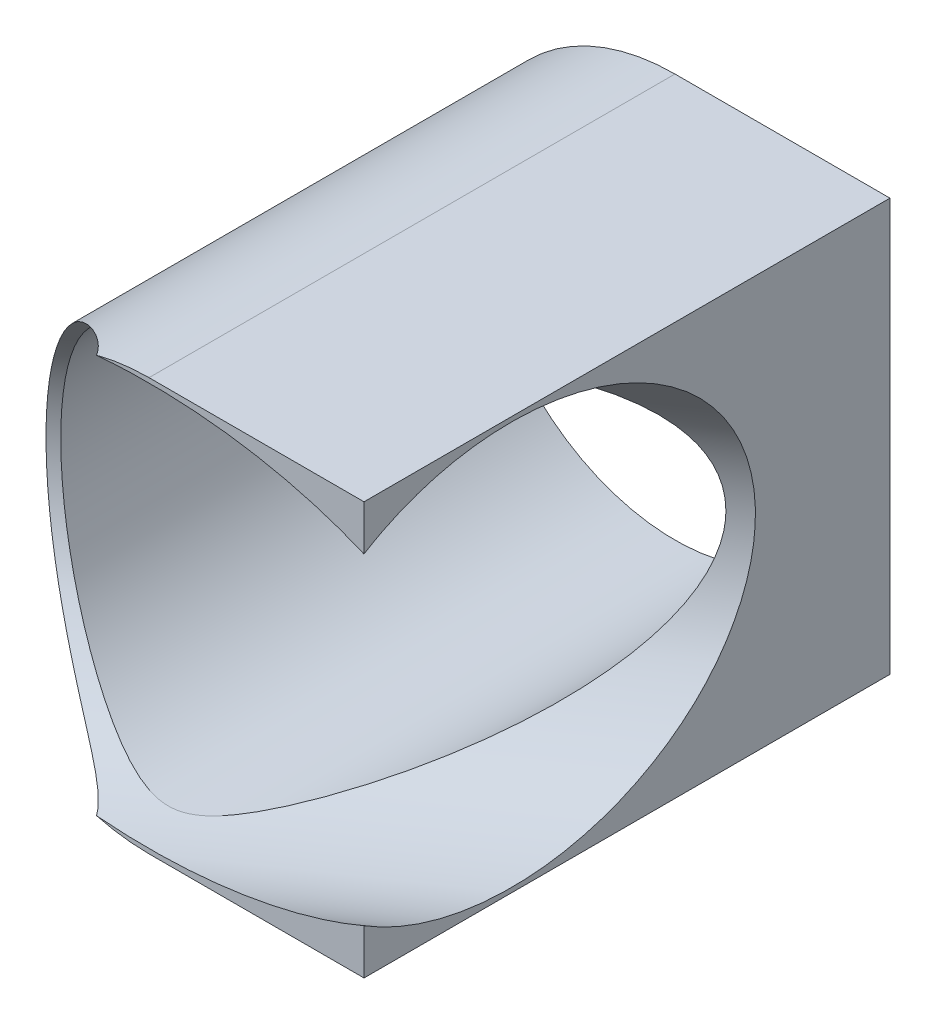
SolidWorks part; units mm, degrees
ref_plane "Front Plane" through (0, 0, 0) normal (0, 0, 1) x (1, 0, 0)
ref_plane "Top Plane" through (0, 0, 0) normal (0, 1, 0) x (1, 0, 0)
ref_plane "Right Plane" through (0, 0, 0) normal (1, 0, 0) x (0, 0, -1)
sketch "Sketch1" plane through (0, 0, 0) normal (0, 0, 1) x (1, 0, 0)
  circle A0 centre (443.1275, 0) radius 22.225 construction
  circle A1 centre (443.1275, 0) radius 22.225 construction
  circle A2 centre (443.1275, 0) radius 23.525
  circle A3 centre (443.1275, 0) radius 22.525
  dimension "D1" = 1.3
  dimension "D2" = 0.3
extrude "Boss-Extrude1" add sketch "Sketch1" against normal blind 60
sketch "Sketch3" plane through (0, 0, -60) normal (0, 0, -1) x (-1, 0, 0)
  line L0 (-443.1275, -23.525) -> (-466.6525, -23.525)
  line L1 (-466.6525, -23.525) -> (-466.6525, 0)
  line L2 (-466.6525, 0) -> (-466.6525, 23.525)
  line L3 (-466.6525, 23.525) -> (-443.1275, 23.525)
  line L5 (-466.6525, 23.525) -> (-467.6525, 23.525)
  line L6 (-466.6525, 23.525) -> (-466.6525, -23.525)
  line L7 (-466.6525, -23.525) -> (-467.6525, -23.525)
  line L8 (-467.6525, 23.525) -> (-467.6525, -23.525)
  circle A0 centre (-443.1275, 0) radius 23.525 construction
  circle M3 centre (-443.1275, 0) radius 23.525
  dimension "D1" = 1
extrude "Boss-Extrude2" add sketch "Sketch3" against normal blind 60 contours L1 L0 M3 | L5 L8 L7 L1 L2 | L3 L2 M3
sketch "Sketch2" plane through (254.325, 0, -174.0591) normal (-0.8252, 0, 0.5648) x (0.5648, 0, 0.8252)
  circle A0 centre (250.2733, 0) radius 23 construction
  circle A1 centre (250.2733, 0) radius 23
extrude "Cut-Extrude1" cut sketch "Sketch2" against normal through all
